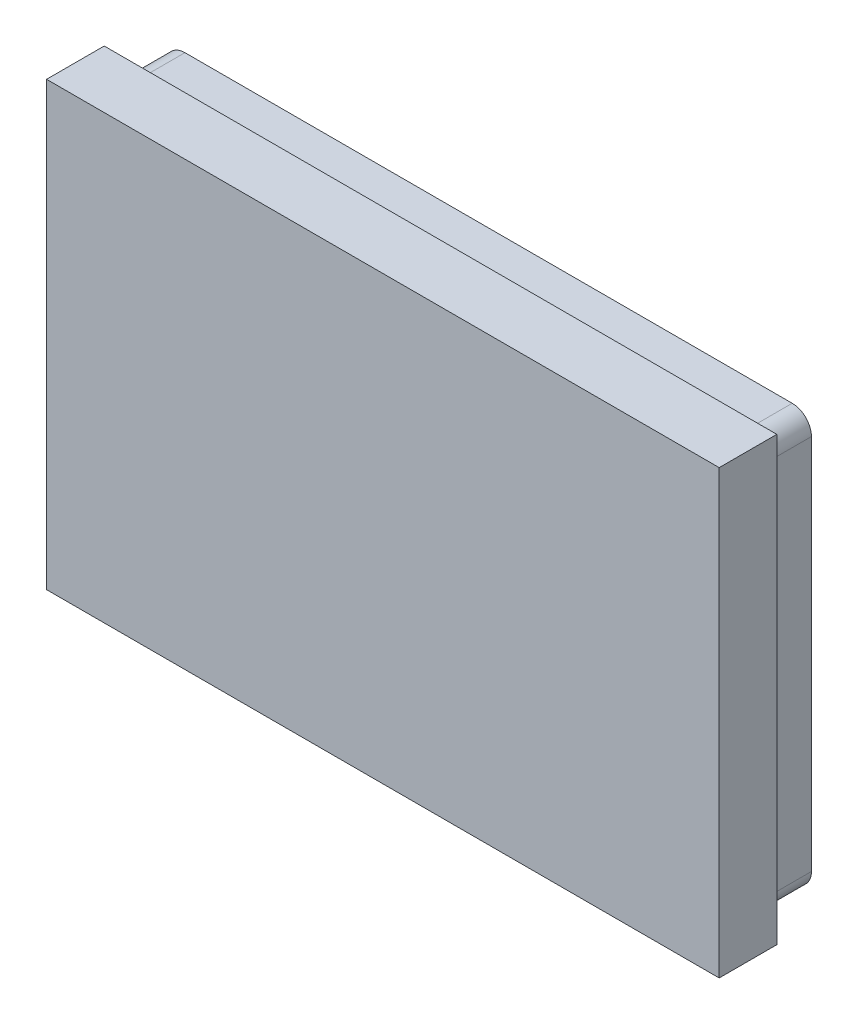
SolidWorks part; units mm, degrees
ref_plane "Plan de face" through (0, 0, 0) normal (0, 0, 1) x (1, 0, 0)
ref_plane "Plan de dessus" through (0, 0, 0) normal (0, 1, 0) x (1, 0, 0)
ref_plane "Plan de droite" through (0, 0, 0) normal (1, 0, 0) x (0, 0, -1)
sketch "Esquisse3" plane through (0, 0, 0) normal (0, 0, 1) x (1, 0, 0)
  line L0 (0, 0) -> (35, 0)
  line L1 (0, 0) -> (0, 23)
  line L2 (35, 0) -> (35, 23)
  line L3 (0, 23) -> (35, 23)
extrude "Boss.-Extru.1" add sketch "Esquisse3" along normal blind 3
sketch "Esquisse4" plane through (0, 0, 0) normal (0, 0, -1) x (-1, 0, 0)
  line L0 (-35, 0) -> (-35, 23) construction
  line L1 (-33.3, 22.3) -> (-1.7, 22.3)
  line L2 (-34.3, 21.3) -> (-34.3, 1.7)
  line L3 (-33.3, 0.7) -> (-1.7, 0.7)
  line L4 (-0.7, 21.3) -> (-0.7, 1.7)
  line L5 (0, 23) -> (0, 0) construction
  line L6 (-35, 23) -> (0, 23) construction
  line L7 (0, 0) -> (-35, 0) construction
  line L9 (-33, 21.7) -> (-2, 21.7)
  line L10 (-33.7, 21) -> (-33.7, 2)
  line L11 (-33, 1.3) -> (-2, 1.3)
  line L12 (-1.3, 21) -> (-1.3, 2)
  arc A0 (-1.7, 0.7) -> (-0.7, 1.7) centre (-1.7, 1.7) ccw
  arc A1 (-1.7, 22.3) -> (-0.7, 21.3) centre (-1.7, 21.3) cw
  arc A2 (-34.3, 1.7) -> (-33.3, 0.7) centre (-33.3, 1.7) ccw
  arc A3 (-33.3, 22.3) -> (-34.3, 21.3) centre (-33.3, 21.3) ccw
  arc A4 (-33.7, 2) -> (-33, 1.3) centre (-33, 2) ccw
  arc A5 (-2, 1.3) -> (-1.3, 2) centre (-2, 2) ccw
  arc A6 (-2, 21.7) -> (-1.3, 21) centre (-2, 21) cw
  arc A7 (-33, 21.7) -> (-33.7, 21) centre (-33, 21) ccw
  dimension "D5" = 1
  dimension "D10" = 0.7
  dimension "D1" = 0.7
  dimension "D2" = 0.7
  dimension "D3" = 0.7
  dimension "D4" = 0.7
  dimension "D6" = 0.6
  dimension "D7" = 0.6
  dimension "D8" = 0.6
  dimension "D9" = 0.6
extrude "Boss.-Extru.2" add sketch "Esquisse4" along normal blind 2.5
sketch "Esquisse5" plane through (0, 0, 0) normal (0, 0, -1) x (-1, 0, 0)
  text T0 "<b>WE MAKE</b>" font "Consolas" height 5
extrude "Boss.-Extru.3" add sketch "Esquisse5" along normal blind 2.5
sketch "Esquisse7" plane through (0, 0, 0) normal (0, 0, -1) x (-1, 0, 0)
  text T0 "PORN" font "Consolas" height 8.5
extrude "Boss.-Extru.4" add sketch "Esquisse7" along normal blind 2.5
